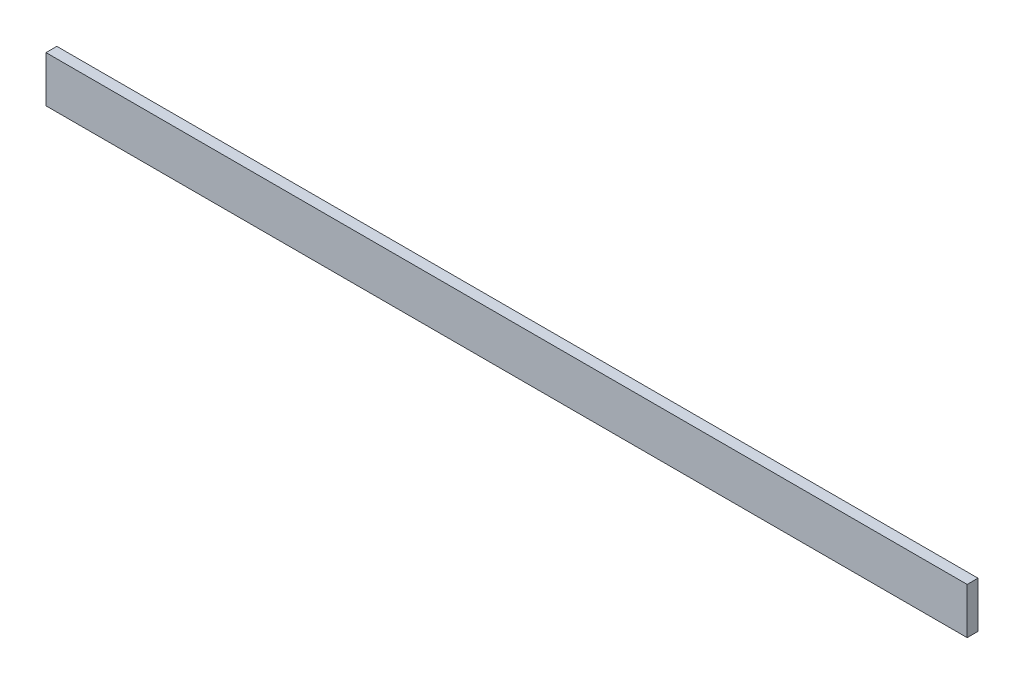
SolidWorks part; units mm, degrees
ref_plane "Front Plane" through (0, 0, 0) normal (0, 0, 1) x (1, 0, 0)
ref_plane "Top Plane" through (0, 0, 0) normal (0, 1, 0) x (1, 0, 0)
ref_plane "Right Plane" through (0, 0, 0) normal (1, 0, 0) x (0, 0, -1)
sketch "Sketch1" plane through (0, 0, 0) normal (0, 0, 1) x (1, 0, 0)
  line L0 (0, 0) -> (0, 50.8)
  line L1 (0, 0) -> (1014.476, 0)
  line L2 (0, 50.8) -> (1014.476, 50.8)
  line L3 (1014.476, 50.8) -> (1014.476, 0)
  dimension "D1" = 50.8
  dimension "D2" = 1014.476
extrude "Boss-Extrude1" add sketch "Sketch1" along normal blind 11.938
